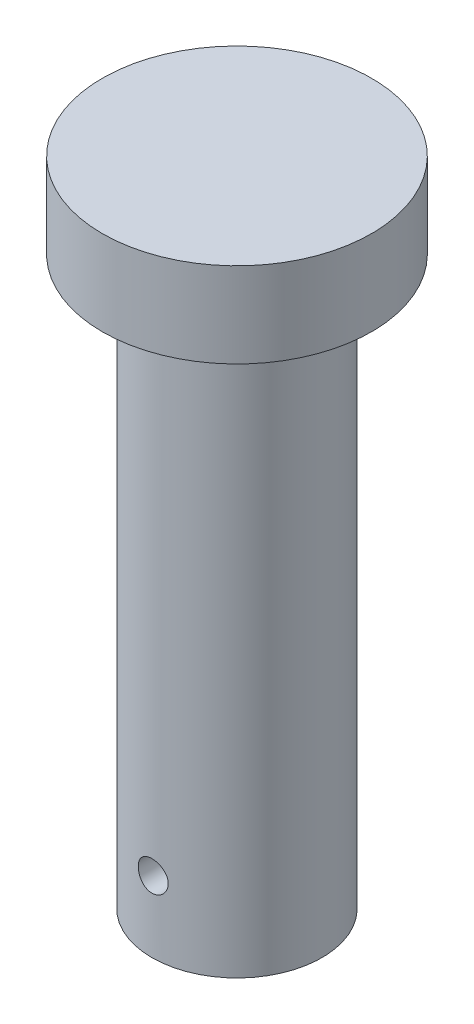
SolidWorks part; units mm, degrees
ref_plane "Front Plane" through (0, 0, 0) normal (0, 0, 1) x (1, 0, 0)
ref_plane "Top Plane" through (0, 0, 0) normal (0, 1, 0) x (1, 0, 0)
ref_plane "Right Plane" through (0, 0, 0) normal (1, 0, 0) x (0, 0, -1)
sketch "Sketch1" plane through (0, 0, 0) normal (0, 1, 0) x (1, 0, 0)
  circle A0 centre (0, 0) radius 19
  dimension "D1" = 38
extrude "Boss-Extrude1" add sketch "Sketch1" along normal blind 12
sketch "Sketch2" plane through (0, 0, 0) normal (0, -1, 0) x (1, 0, 0)
  circle A0 centre (0, 0) radius 12
  dimension "D1" = 24
extrude "Boss-Extrude2" add sketch "Sketch2" along normal blind 80
ref_plane "Plane1" through (0, -70, 0) normal (0, -1, 0) x (-1, 0, 0)
sketch "Sketch3" plane through (0, -70, 0) normal (0, -1, 0) x (-1, 0, 0)
  line L0 (0, 23.7468) -> (0, -26.3415) construction
  line L1 (0, 22) -> (0, -22)
  line L2 (0, -22) -> (2, -22)
  line L3 (2, -22) -> (2.5, 22)
  line L4 (2.5, 22) -> (0, 22)
  dimension "D1" = 44
  dimension "D2" = 22
  dimension "D3" = 2
  dimension "D4" = 2.5
revolve "Cut-Revolve1" cut sketch "Sketch3" angle 360 about L0
